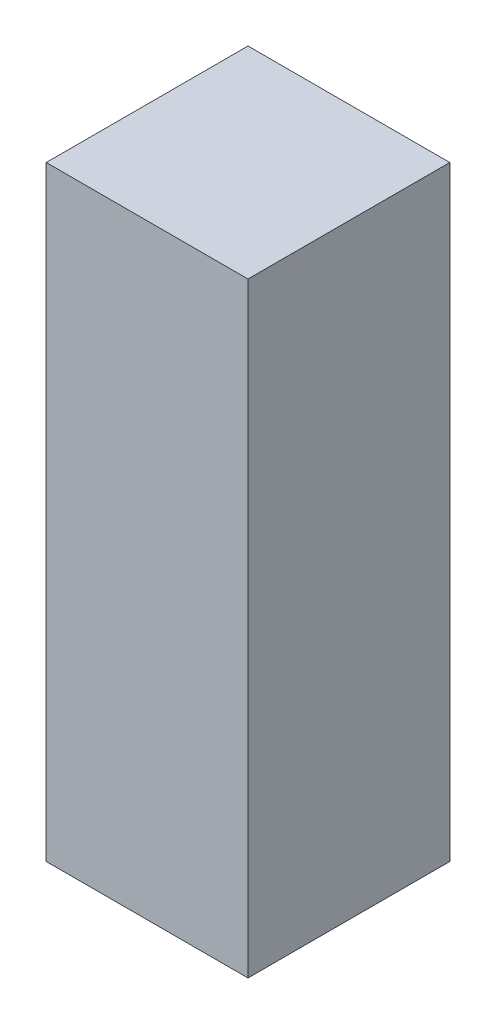
SolidWorks part; units mm, degrees
ref_plane "Front Plane" through (0, 0, 0) normal (0, 0, 1) x (1, 0, 0)
ref_plane "Top Plane" through (0, 0, 0) normal (0, 1, 0) x (1, 0, 0)
ref_plane "Right Plane" through (0, 0, 0) normal (1, 0, 0) x (0, 0, -1)
sketch "Sketch1" plane through (0, 0, 0) normal (0, 0, 1) x (1, 0, 0)
  line L1 (-5, -15) -> (5, -15)
  line L2 (-5, -15) -> (-5, 15)
  line L3 (-5, 15) -> (5, 15)
  line L4 (5, -15) -> (5, 15)
  line L5 (-5, -15) -> (5, 15) construction
  line L6 (-5, 15) -> (5, -15) construction
  point P0 (0, 0)
  dimension "D1" = 30
  dimension "D2" = 10
extrude "BODY" add sketch "Sketch1" along normal blind 10
